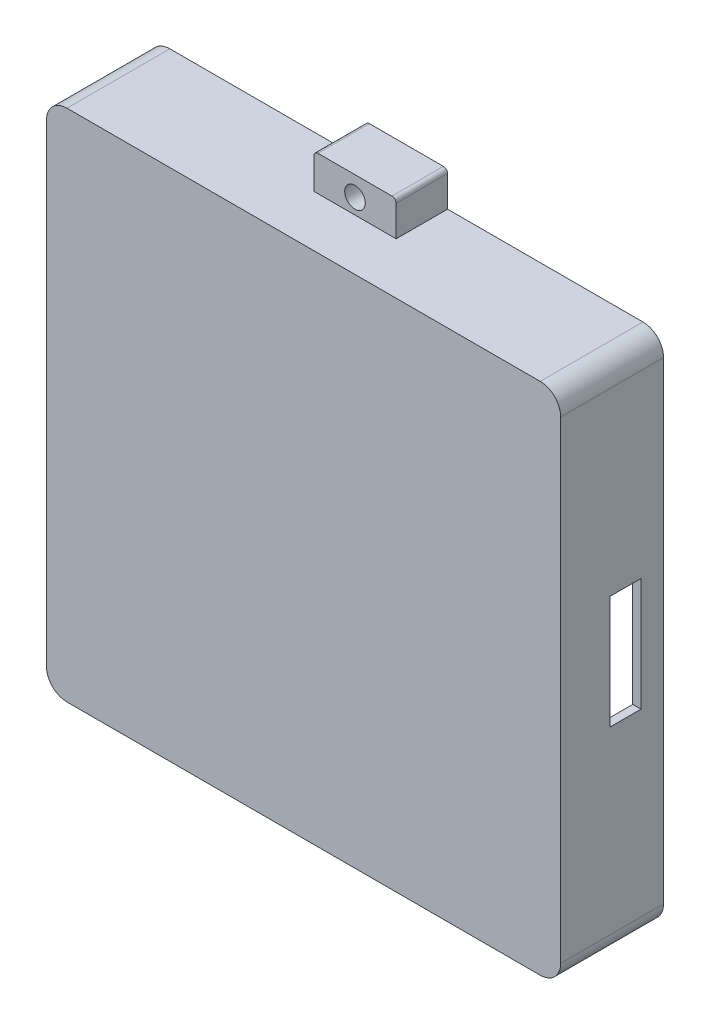
SolidWorks part; units mm, degrees
other "Markup1"
sketch "Sketch10" plane through (0, 167, 0) normal (-0.3497, 0.4547, -0.8191) x (-0.3409, 0.7526, 0.5633)
ref_plane "Front Plane" through (0, 0, 0) normal (0, 0, 1) x (1, 0, 0)
ref_plane "Top Plane" through (0, 0, 0) normal (0, 1, 0) x (1, 0, 0)
ref_plane "Right Plane" through (0, 0, 0) normal (1, 0, 0) x (0, 0, -1)
sketch "Sketch1" plane through (0, 0, 0) normal (0, 0, 1) x (1, 0, 0)
  line L1 (0, 0) -> (250, 0)
  line L2 (0, 0) -> (0, 250)
  line L3 (0, 250) -> (250, 250)
  line L4 (250, 0) -> (250, 250)
  dimension "D1" = 250
  dimension "D2" = 250
extrude "Boss-Extrude1" add sketch "Sketch1" along normal blind 50
sketch "Sketch5" plane through (0, 0, 0) normal (0, 0, 1) x (1, 0, 0)
  line L0 (105, 250) -> (105, 265)
  line L1 (250, 250) -> (0, 250) construction
  line L2 (107, 267) -> (143, 267)
  line L3 (145, 265) -> (145, 250)
  line L4 (250, 250) -> (0, 250) construction
  line L5 (105, 250) -> (145, 250)
  arc A0 (145, 265) -> (143, 267) centre (143, 265) ccw
  arc A1 (107, 267) -> (105, 265) centre (107, 265) ccw
  point P12 (125, 250)
  dimension "D1" = 2
  dimension "D2" = 15
  dimension "D3" = 20
  dimension "D4" = 20
extrude "Boss-Extrude2" add sketch "Sketch5" along normal blind 25
ref_plane "Plane9" through (0, 125, 0) normal (0, 1, 0) x (1, 0, 0)
mirror "Mirror1" about plane through (0, 125, 0) normal (0, 1, 0) of "Boss-Extrude2"
sketch "Sketch8" plane through (0, 0, 0) normal (0, 0, -1) x (-1, 0, 0)
  line L0 (27.5, 125) -> (-27.5, 125) construction
  line L1 (-145, -7.5) -> (-105, -7.5) construction
  line L2 (-145, 0) -> (-145, -15) construction
  line L3 (-105, -15) -> (-105, 0) construction
  circle A0 centre (-125, -7.5) radius 5
  circle A1 centre (-125, 257.5) radius 5
  dimension "D1" = 10
  dimension "D2" = 20
  dimension "D3" = 20
extrude "Cut-Extrude1" cut sketch "Sketch8" against normal blind 25
sketch "Sketch9" plane through (0, 0, 0) normal (0, 0, -1) x (-1, 0, 0)
  line L4 (-246, 246) -> (-246, 4)
  line L17 (-246, 4) -> (-4, 4)
  line L18 (-4, 246) -> (-4, 4)
  line L19 (-246, 246) -> (-4, 246)
extrude "Cut-Extrude4" cut sketch "Sketch9" against normal blind 46
sketch "Sketch14" plane through (0, 0, 0) normal (0, 0, -1) x (-1, 0, 0)
  line L0 (-4, 49) -> (-54, 49)
  line L2 (-4, 4) -> (-4, 246) construction
  line L4 (-54, 49) -> (-54, 4)
  line L5 (-246, 4) -> (-4, 4) construction
  dimension "D1" = 50
  dimension "D2" = 45
extrude "Extrude-Thin2" add sketch "Sketch14" against normal blind 46 thin
sketch "Sketch15" plane through (0, 0, 0) normal (-1, 0, 0) x (0, 0, 1)
  line L0 (50, 250) -> (50, 0) construction
  line L1 (50, 0) -> (0, 0) construction
  circle A0 centre (26, 24) radius 11
  dimension "D3" = 22
  dimension "D1" = 24
  dimension "D2" = 24
extrude "Cut-Extrude5" cut sketch "Sketch15" against normal blind 4
sketch "Sketch17" plane through (250, 0, 0) normal (1, 0, 0) x (0, 0, -1)
  line L0 (-50, 0) -> (-50, 250) construction
  line L1 (-11, 152.5) -> (-26, 152.5)
  line L2 (-11, 152.5) -> (-11, 97.5)
  line L3 (-11, 97.5) -> (-26, 97.5)
  line L4 (-26, 152.5) -> (-26, 97.5)
  line L5 (-50, 0) -> (0, 0) construction
  dimension "D1" = 15
  dimension "D2" = 24
  dimension "D3" = 55
  dimension "D4" = 97.5
extrude "Cut-Extrude7" cut sketch "Sketch17" against normal blind 4
sketch "Sketch18" plane through (0, 51.5, 0) normal (0, 1, 0) x (1, 0, 0)
  line L0 (4, -46) -> (56.5, -46) construction
  line L1 (35.5, -46) -> (45.5, -46)
  line L2 (35.5, -46) -> (35.5, -29.5)
  line L3 (35.5, -29.5) -> (45.5, -29.5)
  line L4 (45.5, -46) -> (45.5, -29.5)
  line L5 (56.5, -46) -> (56.5, 0) construction
  dimension "D1" = 11
  dimension "D2" = 10
  dimension "D3" = 16.5
extrude "Cut-Extrude8" cut sketch "Sketch18" against normal blind 2.5
fillet "Fillet1" radius 10 4 edges at (0, 0, 25) (250, 0, 25) (250, 250, 25) (0, 250, 25)
fillet "Fillet2" radius 10 4 edges at (4, 4, 23) (4, 246, 23) (246, 246, 23) (246, 4, 23)
